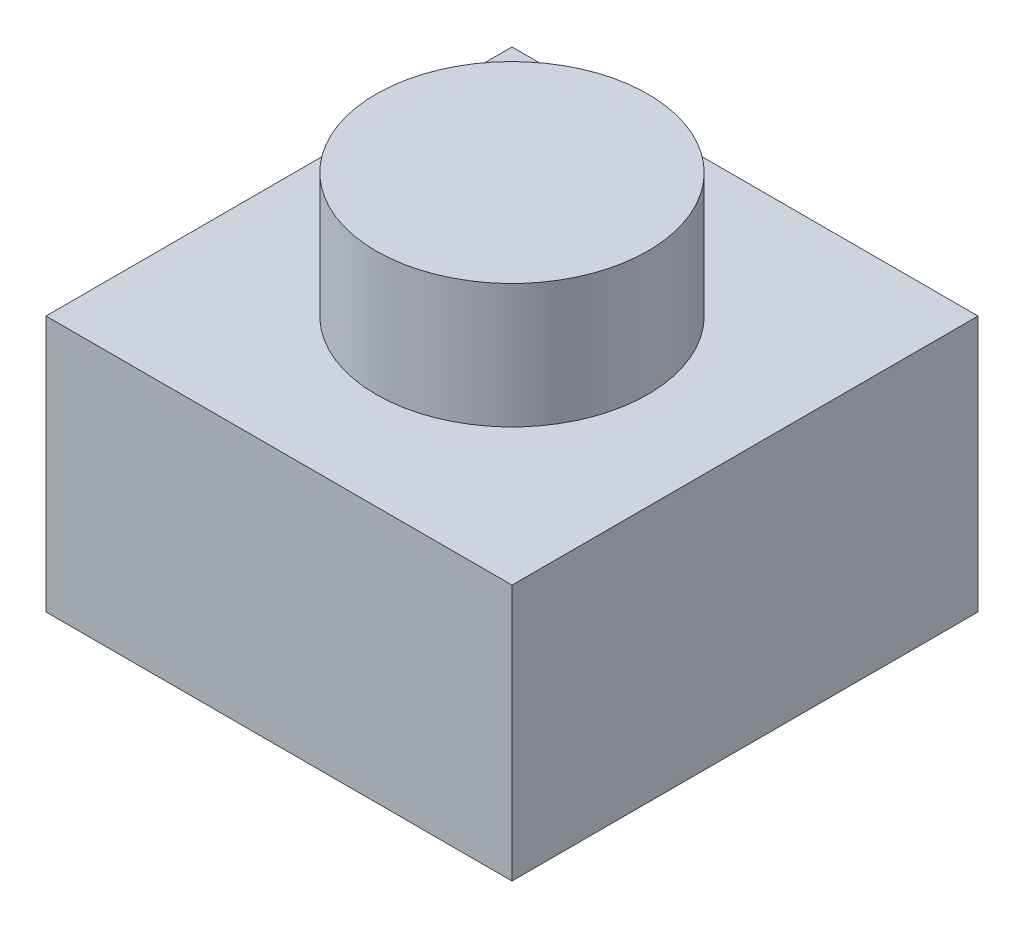
SolidWorks part; units mm, degrees
ref_plane "Спереди" through (0, 0, 0) normal (0, 0, 1) x (1, 0, 0)
ref_plane "Сверху" through (0, 0, 0) normal (0, 1, 0) x (1, 0, 0)
ref_plane "Справа" through (0, 0, 0) normal (1, 0, 0) x (0, 0, -1)
sketch "Sketch1" plane through (0, 0, 0) normal (0, 1, 0) x (1, 0, 0)
  line L1 (3, -3) -> (-3, -3)
  line L2 (3, -3) -> (3, 3)
  line L3 (3, 3) -> (-3, 3)
  line L4 (-3, -3) -> (-3, 3)
  line L5 (3, -3) -> (-3, 3) construction
  line L6 (3, 3) -> (-3, -3) construction
  point P0 (0, 0)
  dimension "D1" = 6
extrude "Boss-Extrude1" add sketch "Sketch1" along normal blind 3.3
sketch "Sketch2" plane through (0, 3.3, 0) normal (0, 1, 0) x (1, 0, 0)
  line L0 (0, -3) -> (0, 3) construction
  line L1 (-3, -3) -> (3, -3) construction
  line L2 (3, 3) -> (-3, 3) construction
  circle A0 centre (0, 0) radius 1.75
  dimension "D1" = 3.5
extrude "Boss-Extrude2" add sketch "Sketch2" along normal blind 1.6
